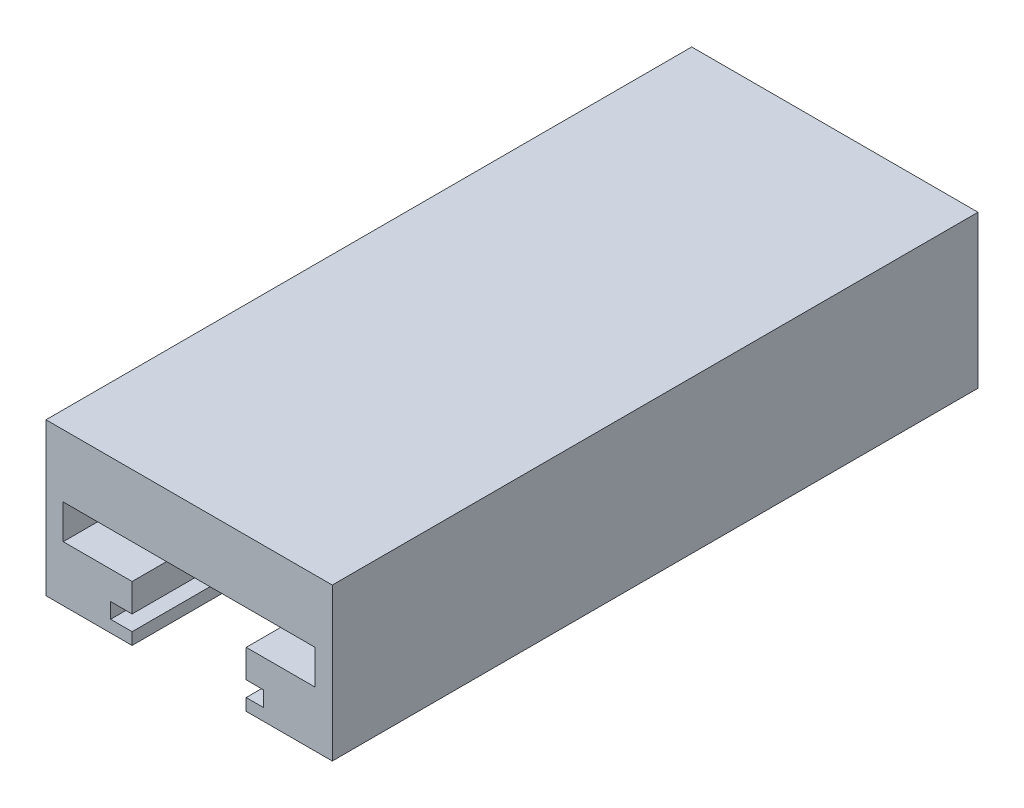
SolidWorks part; units mm, degrees
ref_plane "Front Plane" through (0, 0, 0) normal (0, 0, 1) x (1, 0, 0)
ref_plane "Top Plane" through (0, 0, 0) normal (0, 1, 0) x (1, 0, 0)
ref_plane "Right Plane" through (0, 0, 0) normal (1, 0, 0) x (0, 0, -1)
sketch "Sketch1" plane through (0, 0, 0) normal (0, 0, 1) x (1, 0, 0)
  line L0 (-23.25, 14.536) -> (10, 14.536)
  line L1 (10, 14.536) -> (10, -3.1693)
  line L2 (10, -3.1693) -> (0, -3.1693)
  line L3 (0, -1.78) -> (0, -3.1693)
  line L4 (2, -1.78) -> (0, -1.78)
  line L5 (2, 0) -> (0, 0)
  line L6 (0, 0) -> (0, 3.27)
  line L7 (0, 3.27) -> (8, 3.27)
  line L8 (8, 3.27) -> (8, 7.27)
  line L9 (8, 7.27) -> (0, 7.27)
  line L10 (2, 0) -> (2, -1.78)
  line L11 (0, 7.27) -> (-13.25, 7.27)
  line L12 (-13.25, 7.27) -> (-21.25, 7.27)
  line L13 (-21.25, 7.27) -> (-21.25, 3.27)
  line L14 (-21.25, 3.27) -> (-13.25, 3.27)
  line L15 (-13.25, 3.27) -> (-13.25, 0)
  line L16 (-13.25, 0) -> (-15.7465, 0)
  line L17 (-15.7465, 0) -> (-15.7465, -1.78)
  line L18 (-15.7465, -1.78) -> (-13.25, -1.78)
  line L19 (-13.25, -1.78) -> (-13.25, -3.1693)
  line L20 (-13.25, -3.1693) -> (-23.25, -3.1693)
  line L21 (-23.25, -3.1693) -> (-23.25, 14.536)
  dimension "D1" = 13.25
  dimension "D2" = 17.7465
extrude "Boss-Extrude1" add sketch "Sketch1" along normal blind 75
